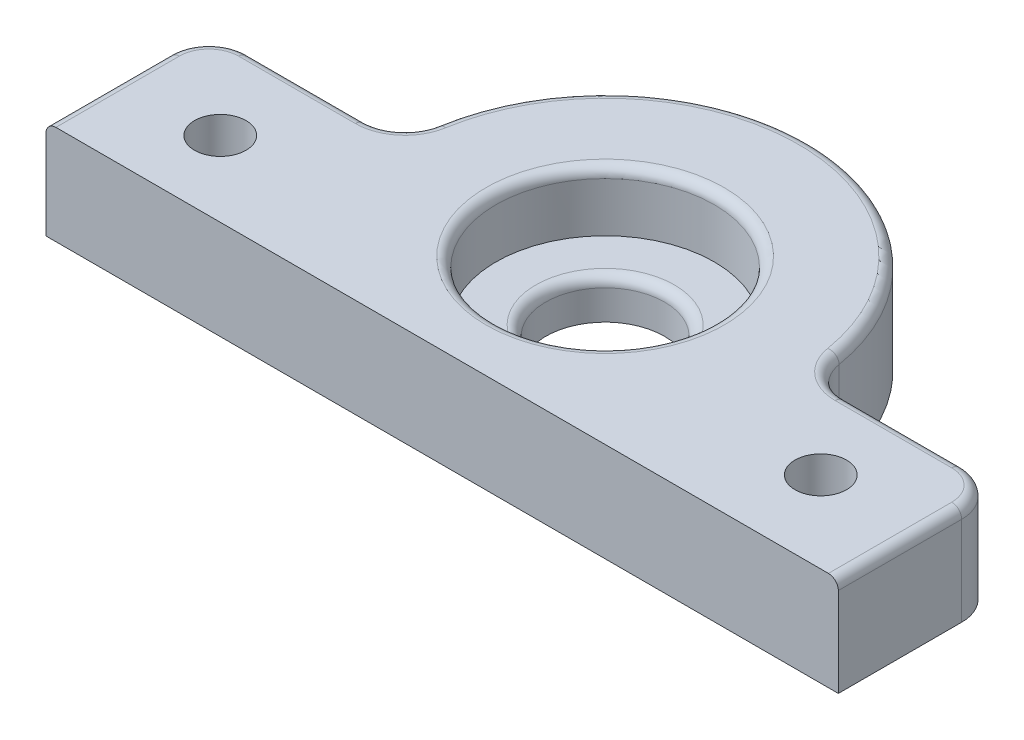
SolidWorks part; units mm, degrees
material "ABS"
ref_plane "Front Plane" through (0, 0, 0) normal (0, 0, 1) x (1, 0, 0)
ref_plane "Top Plane" through (0, 0, 0) normal (0, 1, 0) x (1, 0, 0)
ref_plane "Right Plane" through (0, 0, 0) normal (1, 0, 0) x (0, 0, -1)
sketch "Sketch1" plane through (0, 0, 0) normal (0, 1, 0) x (1, 0, 0)
  line L0 (-40, -16.4541) -> (40, -16.4541)
  line L1 (-40, -16.4541) -> (-40, 0)
  line L2 (-40, 0) -> (-20.55, 0)
  line L3 (40, -16.4541) -> (40, 0)
  line L4 (40, 0) -> (20.55, 0)
  circle A0 centre (0, 0) radius 11.025
  arc A1 (20.55, 0) -> (-20.55, 0) centre (0, 0) ccw
  point P6 (0, -16.4541)
  dimension "D1" = 22.05
  dimension "D2" = 9.525
  dimension "D3" = 16.4541
  dimension "D4" = 80
extrude "Boss-Extrude1" add sketch "Sketch1" along normal blind 10
sketch "Sketch3" plane through (0, 0, 0) normal (0, -1, 0) x (1, 0, 0)
  circle A0 centre (0, 0) radius 11.025
  circle A1 centre (0, 0) radius 6
  dimension "D1" = 22.05
  dimension "D2" = 12
extrude "Boss-Extrude2" add sketch "Sketch3" against normal blind 4
fillet "Fillet1" radius 4 4 edges at (-40, 5, 0) (-20.55, 5, 0) (20.55, 5, 0) (40, 5, 0)
fillet "Fillet2" radius 1 11 edges at (0, 10, 11.025) (-21.6342, 10, -0.9498) (0, 10, -20.55) (21.6342, 10, -0.9498) (30.111, 10, 0) (38.8284, 10, 1.1716) (40, 10, 10.2271) (-40, 10, 10.2271) (-38.8284, 10, 1.1716) (-30.111, 10, 0) (0, 4, -6)
sketch "Sketch4" plane through (0, 0, 0) normal (0, -1, 0) x (1, 0, 0)
  line L0 (0, 0) -> (0, 16.4541) construction
  line L1 (-40, 16.4541) -> (40, 16.4541) construction
  circle A0 centre (30, 8.2271) radius 2.6
  circle A1 centre (-29.9966, 8.862) radius 2.6
  point P7 (0, 8.2271)
  dimension "D1" = 5.2
  dimension "D2" = 5.2
  dimension "D3" = 60
  dimension "D4" = 30
extrude "Cut-Extrude1" cut sketch "Sketch4" against normal up to next
equation "\"D4@Sketch4\"=\"D3@Sketch4\"/2"
